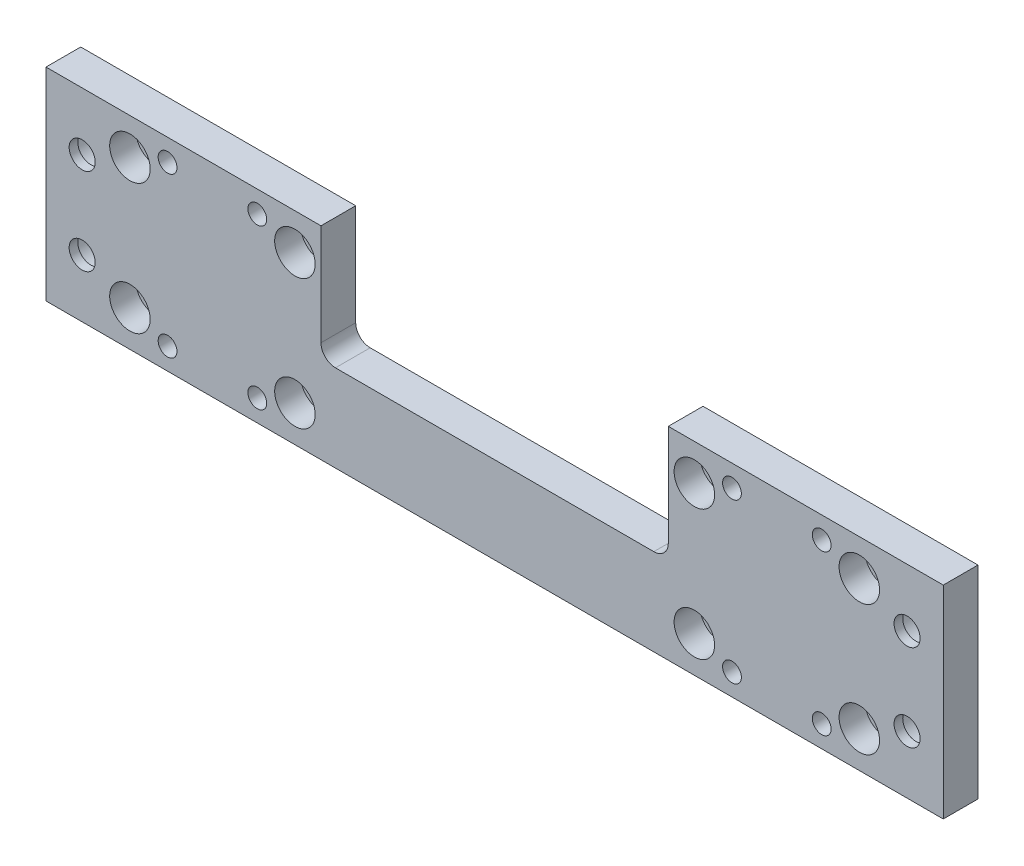
SolidWorks part; units mm, degrees
material "A3钢"
ref_plane "前视基准面" through (0, 0, 0) normal (0, 0, 1) x (1, 0, 0)
ref_plane "上视基准面" through (0, 0, 0) normal (0, 1, 0) x (1, 0, 0)
ref_plane "右视基准面" through (0, 0, 0) normal (1, 0, 0) x (0, 0, -1)
sketch "草图1" plane through (0, 0, 0) normal (0, 0, 1) x (1, 0, 0)
  line L1 (-155, -20) -> (155, -20)
  line L2 (-155, -20) -> (-155, 20)
  line L3 (-155, 20) -> (155, 20)
  line L4 (155, -20) -> (155, 20)
  line L5 (-155, -20) -> (155, 20) construction
  line L6 (-155, 20) -> (155, -20) construction
  point P0 (0, 0)
  dimension "D1" = 40
  dimension "D2" = 310
extrude "凸台-拉伸1" add sketch "草图1" along normal blind 12
sketch "草图8" plane through (0, 0, 12) normal (0, 0, 1) x (1, 0, 0)
  line L0 (0, 45.8201) -> (0, -38.9975) construction
  line L1 (-155, 20) -> (-60, 20)
  line L2 (-155, 20) -> (-155, 35)
  line L3 (-155, 35) -> (-60, 35)
  line L4 (-60, 20) -> (-60, 35)
  line L5 (169.7557, 0) -> (-171.994, 0) construction
  line L6 (60, 20) -> (60, 35)
  line L7 (155, 35) -> (60, 35)
  line L8 (155, 20) -> (155, 35)
  line L9 (155, 20) -> (60, 20)
  line L10 (-155, 20) -> (-155, -20) construction
  line L11 (-155, -35) -> (155, -35)
  line L12 (-155, -35) -> (-155, -20)
  line L13 (-155, -20) -> (155, -20)
  line L14 (155, -35) -> (155, -20)
  dimension "D1" = 120
  dimension "D2" = 15
  dimension "D3" = 15
extrude "凸台-拉伸2" add sketch "草图8" against normal up to surface (12 mm away) up to face at (0, 0, 0)
hole_wizard "打孔尺寸(%根据)内六角圆柱头螺钉的类型2" positions "草图2" profile "草图3" counterbore size "M8" standard "GB" end condition through all
sketch "草图2" plane through (0, 0, 12) normal (0, 0, 1) x (1, 0, 0)
  line L0 (-162.1918, 0) -> (167.955, 0) construction
  line L3 (0, 46.3111) -> (0, -44.2529) construction
  point P0 (-126, 22.5)
  point P2 (-69, 22.5)
  point P17 (-69, -22.5)
  point P18 (-126, -22.5)
  point P19 (126, -22.5)
  point P20 (69, -22.5)
  point P21 (69, 22.5)
  point P22 (126, 22.5)
  dimension "D1" = 138
  dimension "D2" = 57
  dimension "D3" = 45
sketch "草图3" plane through (-126, 22.5, 12) normal (1, 0, 0) x (0, -1, 0)
  line L0 (0, 0) -> (0, 12)
  line L1 (0, 12) -> (4.5, 12)
  line L3 (4.5, 12) -> (4.5, 9)
  line L4 (4.5, 9) -> (7, 9)
  line L5 (7, 9) -> (7, 0)
  line L7 (7, 0) -> (0, 0)
  line L11 (0, -6.35) -> (0, 107.95) construction
  dimension "通孔孔直径" = 9
  dimension "通孔孔深度" = 12
  dimension "柱形沉头孔直径" = 14
  dimension "柱形沉头孔深度" = 9
hole_wizard "打孔尺寸(%根据)内六角圆柱头螺钉的类型2" positions "草图4" profile "草图5" counterbore size "M8" standard "GB" end condition through all
sketch "草图4" plane through (0, 0, 0) normal (0, 0, -1) x (-1, 0, 0)
  line L0 (0, 34.073) -> (0, -34.899) construction
  line L3 (21.0633, 0) -> (-122.2499, 0) construction
  point P0 (-142.5, 15)
  point P2 (-142.5, -15)
  point P12 (142.5, -15)
  point P13 (142.5, 15)
  dimension "D1" = 285
  dimension "D2" = 30
sketch "草图5" plane through (142.5, 15, 0) normal (1, 0, 0) x (0, 1, 0)
  line L0 (0, 0) -> (0, 12)
  line L1 (0, 12) -> (4.5, 12)
  line L3 (4.5, 12) -> (4.5, 9)
  line L4 (4.5, 9) -> (7, 9)
  line L5 (7, 9) -> (7, 0)
  line L7 (7, 0) -> (0, 0)
  line L11 (0, -6.35) -> (0, 107.95) construction
  dimension "通孔孔直径" = 9
  dimension "通孔孔深度" = 12
  dimension "柱形沉头孔直径" = 14
  dimension "柱形沉头孔深度" = 9
hole_wizard "打孔尺寸(%根据)内六角圆柱头螺钉的类型3" positions "草图9" profile "草图10" counterbore size "M6" standard "GB" end condition through all
sketch "草图9" plane through (0, 0, 0) normal (0, 0, -1) x (-1, 0, 0)
  line L0 (-160.3996, 0) -> (165.1554, 0) construction
  line L3 (0, 53.3945) -> (0, -58.1503) construction
  point P0 (-82, 27.5)
  point P2 (-113, 27.5)
  point P16 (-113, -27.5)
  point P17 (-82, -27.5)
  point P18 (82, -27.5)
  point P19 (113, -27.5)
  point P20 (113, 27.5)
  point P21 (82, 27.5)
  dimension "D1" = 164
  dimension "D2" = 31
  dimension "D3" = 55
sketch "草图10" plane through (82, 27.5, 0) normal (1, 0, 0) x (0, 1, 0)
  line L0 (0, 0) -> (0, 12)
  line L1 (0, 12) -> (3.25, 12)
  line L3 (3.25, 12) -> (3.25, 7)
  line L4 (3.25, 7) -> (5.5, 7)
  line L5 (5.5, 7) -> (5.5, 0)
  line L7 (5.5, 0) -> (0, 0)
  line L11 (0, -6.35) -> (0, 107.95) construction
  dimension "通孔孔直径" = 6.5
  dimension "通孔孔深度" = 12
  dimension "柱形沉头孔直径" = 11
  dimension "柱形沉头孔深度" = 7
sketch "草图11" plane through (0, 0, 12) normal (0, 0, 1) x (1, 0, 0)
  line L0 (60, 20) -> (-60, 20) construction
  line L1 (-60, 20) -> (60, 20)
  line L2 (-60, 20) -> (-60, 0)
  line L3 (-55, -5) -> (55, -5)
  line L4 (60, 20) -> (60, 0)
  line L5 (0, 28.4835) -> (0, -33.3372) construction
  arc A0 (55, -5) -> (60, 0) centre (55, 0) ccw
  arc A1 (-60, 0) -> (-55, -5) centre (-55, 0) ccw
  point P12 (60, -5)
  point P15 (-60, -5)
  dimension "D3" = 5
  dimension "D1" = 25
extrude "切除-拉伸1" cut sketch "草图11" against normal through all
